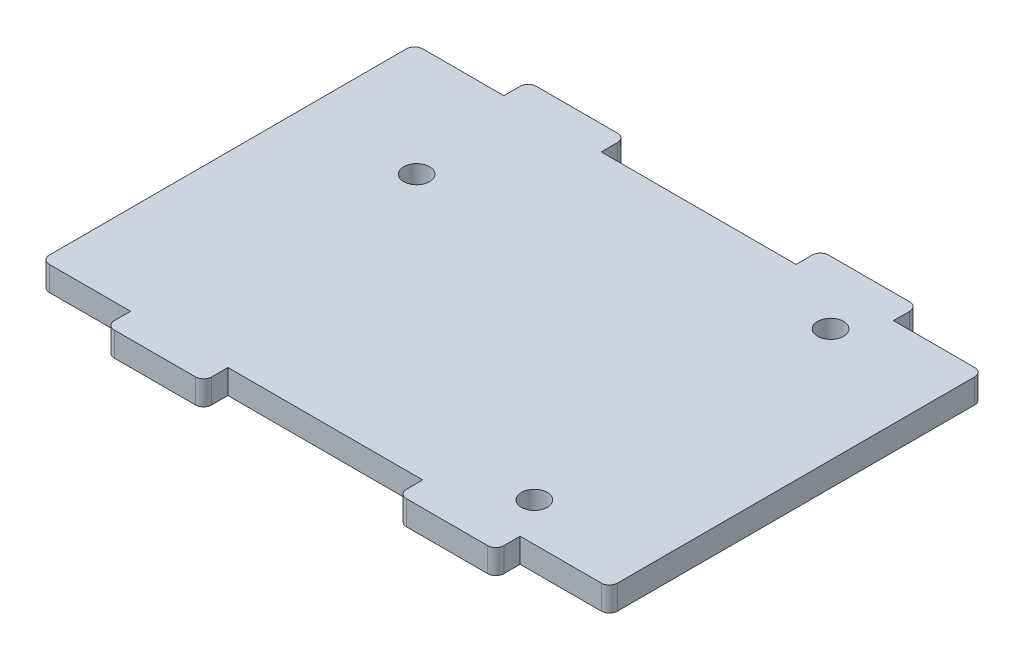
SolidWorks part; units mm, degrees
ref_plane "前视" through (0, 0, 0) normal (0, 0, 1) x (1, 0, 0)
ref_plane "上视" through (0, 0, 0) normal (0, 1, 0) x (1, 0, 0)
ref_plane "右视" through (0, 0, 0) normal (1, 0, 0) x (0, 0, -1)
sketch "草图1" plane through (0, 0, 0) normal (0, 1, 0) x (1, 0, 0)
  line L1 (-35, 26) -> (35, 26)
  line L2 (-35, 26) -> (-35, -26)
  line L3 (-35, -26) -> (35, -26)
  line L4 (35, 26) -> (35, -26)
  line L5 (-35, 26) -> (35, -26) construction
  line L6 (-35, -26) -> (35, 26) construction
  point P0 (0, 0)
  dimension "D1" = 70
  dimension "D2" = 52
extrude "凸台-拉伸1" add sketch "草图1" along normal blind 3
sketch "草图2" plane through (0, 3, 0) normal (0, 1, 0) x (1, 0, 0)
  line L0 (0, 28.3833) -> (0, -5.0471) construction
  line L1 (35, 26) -> (-35, 26) construction
  line L2 (-12, 29) -> (12, 29)
  line L3 (-12, 29) -> (-12, 23)
  line L4 (-12, 23) -> (12, 23)
  line L5 (12, 29) -> (12, 23)
  line L6 (-12, 29) -> (12, 23) construction
  line L7 (-12, 23) -> (12, 29) construction
  line L8 (-35, 26) -> (-24, 26)
  line L9 (-24, 26) -> (-24, 23)
  line L10 (-24, 23) -> (-35, 23)
  line L11 (-35, 26) -> (-35, -26) construction
  line L12 (-35, 23) -> (-35, 26)
  line L13 (35, 26) -> (24, 26)
  line L14 (24, 26) -> (24, 23)
  line L15 (24, 23) -> (35, 23)
  line L16 (35, -26) -> (35, 26) construction
  line L17 (35, 23) -> (35, 26)
  line L18 (0, 0) -> (-5.0038, 0) construction
  line L19 (-35, -23) -> (-35, -26)
  line L20 (-35, -26) -> (-24, -26)
  line L21 (-24, -26) -> (-24, -23)
  line L22 (-24, -23) -> (-35, -23)
  line L23 (35, -23) -> (35, -26)
  line L24 (24, -23) -> (35, -23)
  line L25 (24, -26) -> (24, -23)
  line L26 (35, -26) -> (24, -26)
  line L27 (-12, -29) -> (-12, -23)
  line L28 (-12, -23) -> (12, -23)
  line L29 (12, -29) -> (12, -23)
  line L30 (-12, -29) -> (12, -29)
  circle A0 centre (-21, 9.25) radius 1.6
  circle A1 centre (21, 18.25) radius 1.6
  circle A2 centre (21, -18.25) radius 1.6
  point P3 (0, 26)
  dimension "D7" = 14
  dimension "D9" = 42
  dimension "D1" = 6
  dimension "D2" = 24
  dimension "D3" = 11
  dimension "D4" = 3
  dimension "D5" = 3
  dimension "D6" = 11
  dimension "D8" = 13.75
  dimension "D10" = 42
  dimension "D11" = 4.75
  dimension "D12" = 4.75
extrude "切除-拉伸1" cut sketch "草图2" against normal through all
fillet "圆角1" radius 1 12 edges at (-12, 1.5, -26) (12, 1.5, -26) (24, 1.5, -26) (35, 1.5, -23) (35, 1.5, 23) (24, 1.5, 26) (12, 1.5, 26) (-12, 1.5, 26) (-24, 1.5, 26) (-35, 1.5, 23) (-35, 1.5, -23) (-24, 1.5, -26)
